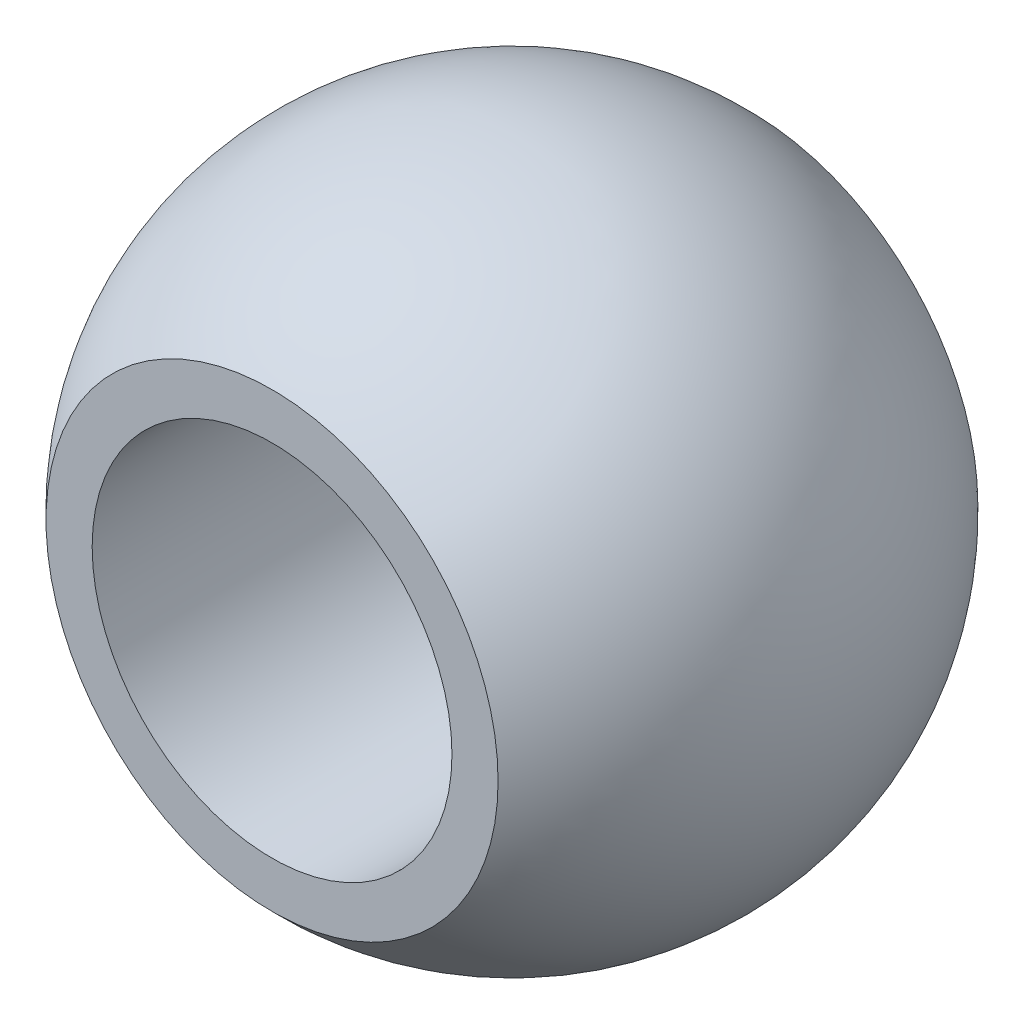
SolidWorks part; units mm, degrees
material "Plain Carbon Steel"
ref_plane "Front Plane" through (0, 0, 0) normal (0, 0, 1) x (1, 0, 0)
ref_plane "Top Plane" through (0, 0, 0) normal (0, 1, 0) x (1, 0, 0)
ref_plane "Right Plane" through (0, 0, 0) normal (1, 0, 0) x (0, 0, -1)
sketch "Sketch1" plane through (0, 0, 0) normal (1, 0, 0) x (0, 0, -1)
  line L0 (0, 0) -> (0, 61.9768) construction
  line L1 (-31.259, 0) -> (29.384, 0) construction
  line L2 (-6.35, 5.9834) -> (-6.35, 4.7625)
  line L3 (-6.35, 4.7625) -> (6.35, 4.7625)
  line L4 (6.35, 4.7625) -> (6.35, 5.9834)
  arc A0 (-6.35, 5.9834) -> (6.35, 5.9834) centre (0, 0) cw
  point P7 (0, 8.7249)
  dimension "D2" = 8.7249
  dimension "D1" = 12.7
  dimension "D3" = 4.7625
revolve "Revolve1" add sketch "Sketch1"
sketch "Sketch2" plane through (0, 0, 0) normal (1, 0, 0) x (0, 0, -1)
  line L0 (-11.0989, 0) -> (11.0989, 0) construction
  arc A0 (6.35, 5.9834) -> (-6.35, 5.9834) centre (0, 0) ccw construction
  point P3 (0, 0)
